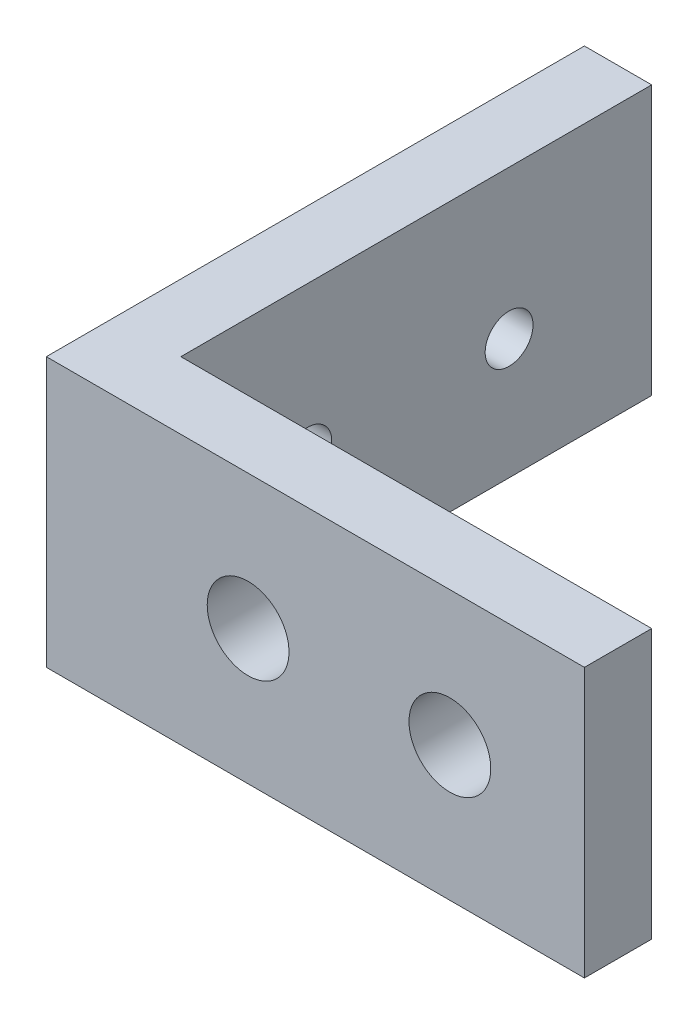
SolidWorks part; units mm, degrees
material "Plain Carbon Steel"
ref_plane "Front Plane" through (0, 0, 0) normal (0, 0, 1) x (1, 0, 0)
ref_plane "Top Plane" through (0, 0, 0) normal (0, 1, 0) x (1, 0, 0)
ref_plane "Right Plane" through (0, 0, 0) normal (1, 0, 0) x (0, 0, -1)
sketch "Sketch1" plane through (0, 0, 0) normal (0, 1, 0) x (1, 0, 0)
  line L0 (-9.525, 12.7) -> (-9.525, -9.525)
  line L1 (-12.7, -12.7) -> (12.7, -12.7)
  line L2 (-12.7, -12.7) -> (-12.7, 12.7)
  line L3 (-12.7, 12.7) -> (-9.525, 12.7)
  line L4 (12.7, -12.7) -> (12.7, -9.525)
  line L5 (-12.7, -12.7) -> (89.1204, 89.1204) construction
  line L6 (-12.7, 12.7) -> (12.7, -12.7) construction
  line L7 (-9.525, -9.525) -> (12.7, -9.525)
  point P0 (0, 0)
  dimension "D1" = 3.175
  dimension "D2" = 3.175
  dimension "D3" = 25.4
  dimension "D4" = 25.4
extrude "Boss-Extrude1" add sketch "Sketch1" along normal blind 12.7
sketch "Sketch3" plane through (0, 0, 9.525) normal (0, 0, -1) x (-1, 0, 0)
  line L4 (-12.7, 0) -> (9.525, 0)
  line L5 (9.525, 0) -> (9.525, 12.7)
  line L6 (9.525, 12.7) -> (-12.7, 12.7)
  line L7 (-12.7, 12.7) -> (-12.7, 0)
  line L8 (-12.7, 0) -> (9.525, 0)
  line L9 (9.525, 0) -> (9.525, 12.7)
  line L10 (9.525, 12.7) -> (-12.7, 12.7)
  line L11 (-12.7, 12.7) -> (-12.7, 0)
  point P2 (-6.35, 6.35)
  point P5 (3.175, 6.35)
  dimension "D2" = 6.35
  dimension "D3" = 6.35
  dimension "D4" = 6.35
  dimension "D5" = 9.525
  dimension "D1" = 0
hole_wizard "#24 (0.152) Diameter Hole1" positions "3DSketch1" profile "Sketch5" hole size "#24" standard "ANSI Inch" end condition through all
sketch3d "3DSketch1"
  point P0 (6.35, 6.35, 9.525)
  point P3 (-3.175, 6.35, 9.525)
sketch "Sketch5" plane through (6.35, 6.35, 9.525) normal (1, 0, 0) x (0, 1, 0)
  line L0 (0, 0) -> (0, 3.175)
  line L1 (0, 3.175) -> (1.9304, 3.175)
  line L2 (1.9304, 3.175) -> (1.9304, 0)
  line L5 (1.9304, 0) -> (0, 0)
  line L11 (0, -6.35) -> (0, 107.95) construction
  dimension "Thru Hole Dia." = 3.8608
  dimension "Thru Hole Depth" = 3.175
sketch "Sketch6" plane through (-12.7, 0, 0) normal (-1, 0, 0) x (0, 0, 1)
  line L0 (12.7, 12.7) -> (12.7, 0) construction
  line L1 (-12.7, 12.7) -> (12.7, 12.7) construction
  point P0 (-5.969, 5.6896)
  point P1 (3.5306, 5.6896)
  dimension "D1" = 9.1694
  dimension "D2" = 9.4996
  dimension "D3" = 7.0104
  dimension "D4" = 7.0104
hole_wizard "Tap Drill for #4-40 Tap1" positions "3DSketch2" profile "Sketch7" hole size "#4-40" standard "ANSI Inch" end condition through all
sketch3d "3DSketch2"
  point P0 (-12.7, 5.6896, -5.969)
  point P3 (-12.7, 5.6896, 3.5306)
sketch "Sketch7" plane through (-12.7, 5.6896, -5.969) normal (0, 1, 0) x (0, 0, 1)
  line L0 (0, 0) -> (0, 25.4)
  line L1 (0, 25.4) -> (1.1303, 25.4)
  line L2 (1.1303, 25.4) -> (1.1303, 0)
  line L5 (1.1303, 0) -> (0, 0)
  line L11 (0, -6.35) -> (0, 107.95) construction
  dimension "Thru Hole Dia." = 2.2606
  dimension "Thru Hole Depth" = 25.4
